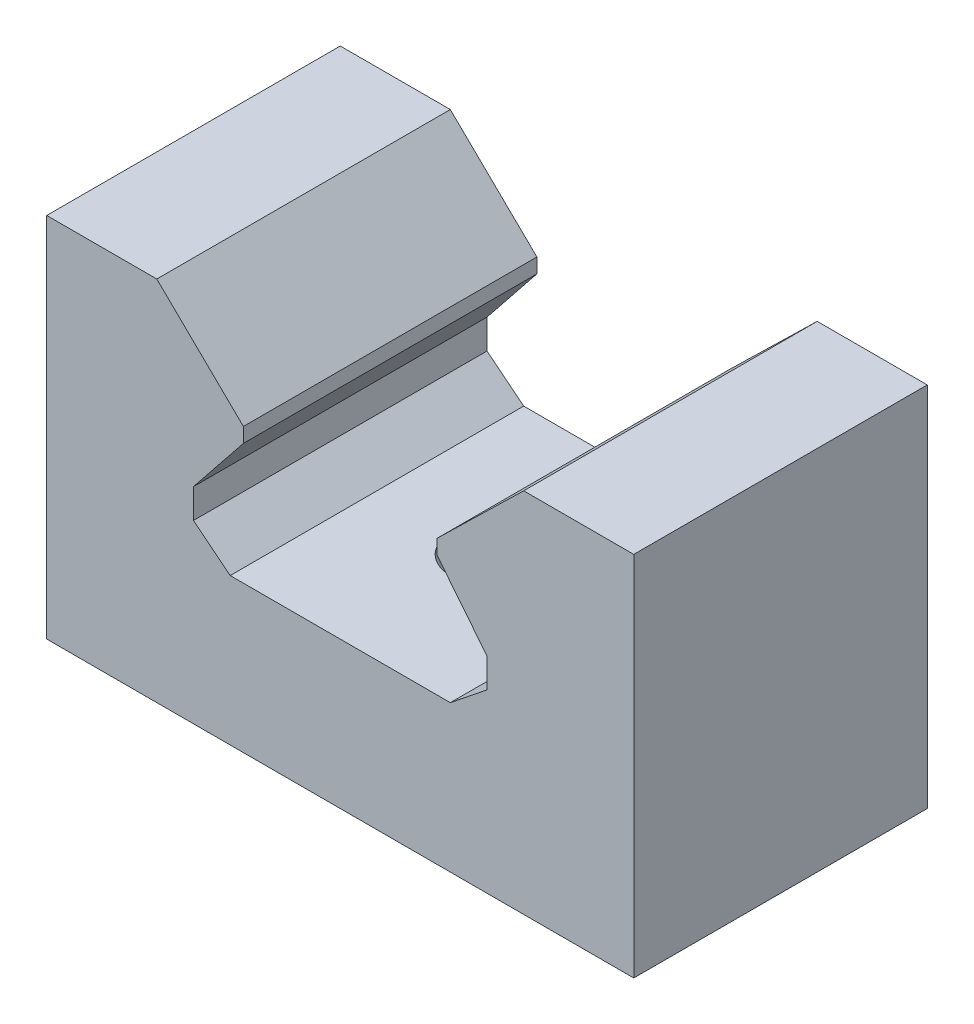
SolidWorks part; units mm, degrees
ref_plane "前视基准面" through (0, 0, 0) normal (0, 0, 1) x (1, 0, 0)
ref_plane "上视基准面" through (0, 0, 0) normal (0, 1, 0) x (1, 0, 0)
ref_plane "右视基准面" through (0, 0, 0) normal (1, 0, 0) x (0, 0, -1)
sketch "草图1" plane through (0, 0, 0) normal (0, 0, 1) x (1, 0, 0)
  line L1 (-20, 12.5) -> (20, 12.5)
  line L2 (-20, 12.5) -> (-20, -12.5)
  line L3 (-20, -12.5) -> (20, -12.5)
  line L4 (20, 12.5) -> (20, -12.5)
  line L5 (-20, 12.5) -> (20, -12.5) construction
  line L6 (-20, -12.5) -> (20, 12.5) construction
  point P0 (0, 0)
  dimension "D1" = 40
  dimension "D2" = 25
extrude "凸台-拉伸1" add sketch "草图1" along normal blind 20
sketch "草图2" plane through (0, 0, 0) normal (0, 0, -1) x (-1, 0, 0)
  line L0 (7.5, -2.5) -> (10, -0.5)
  line L1 (-20, 12.5) -> (20, 12.5) construction
  line L2 (-7.5, -2.5) -> (7.5, -2.5)
  line L3 (10, -0.5) -> (10, 1.5)
  line L4 (0, 0) -> (0, 20.7928) construction
  line L5 (-10, -0.5) -> (-10, 1.5)
  line L6 (-7.5, -2.5) -> (-10, -0.5)
  line L7 (10, 1.5) -> (6.6, 5.75)
  line L8 (6.6, 5.75) -> (6.6, 6.75)
  line L9 (6.6, 6.75) -> (12.5, 12.5)
  line L10 (-6.6, 6.75) -> (-12.5, 12.5)
  line L11 (-6.6, 5.75) -> (-6.6, 6.75)
  line L12 (-10, 1.5) -> (-6.6, 5.75)
  line L13 (-20, -12.5) -> (-20, 12.5) construction
  point P19 (-6, 7.5048)
  point P20 (0, 0)
  point P21 (6, 6.4939)
  dimension "D1" = 15
  dimension "D2" = 15
  dimension "D3" = 20
  dimension "D4" = 20
  dimension "D5" = 2
  dimension "D6" = 13.2
  dimension "D7" = 25
  dimension "D8" = 1
  dimension "D9" = 2
extrude "切除-拉伸1" cut sketch "草图2" against normal blind 20 and the other way through all
ref_plane "基准面1" through (0, 0, 0) normal (1, 0, 0) x (0, 0, -1)
hole_wizard "M6 螺纹孔1" positions "草图3" profile "草图4" tap size "M6" standard "GB"
sketch "草图3" plane through (0, -12.5, 0) normal (0, -1, 0) x (-1, 0, 0)
  line L0 (0, 11) -> (0, -11) construction
  line L1 (20, -20) -> (-20, -20) construction
  point P0 (0, -10)
  dimension "D1" = 10
sketch "草图4" plane through (0, -12.5, 10) normal (1, 0, 0) x (0, 0, -1)
  line L0 (0, 0) -> (0, 19.5022)
  line L1 (0, 19.5022) -> (2.5, 18)
  line L2 (2.5, 18) -> (2.5, 0)
  line L5 (2.5, 0) -> (0, 0)
  line L10 (0, 19.5022) -> (-2.5, 18) construction
  line L11 (0, -6.35) -> (0, 107.95) construction
  dimension "螺纹孔钻头直径" = 5
  dimension "螺纹孔钻头深度" = 18
  dimension "导头角度" = 118
cosmetic thread "孔螺蚊线1" parameters "D1"=12, "D2"=6
